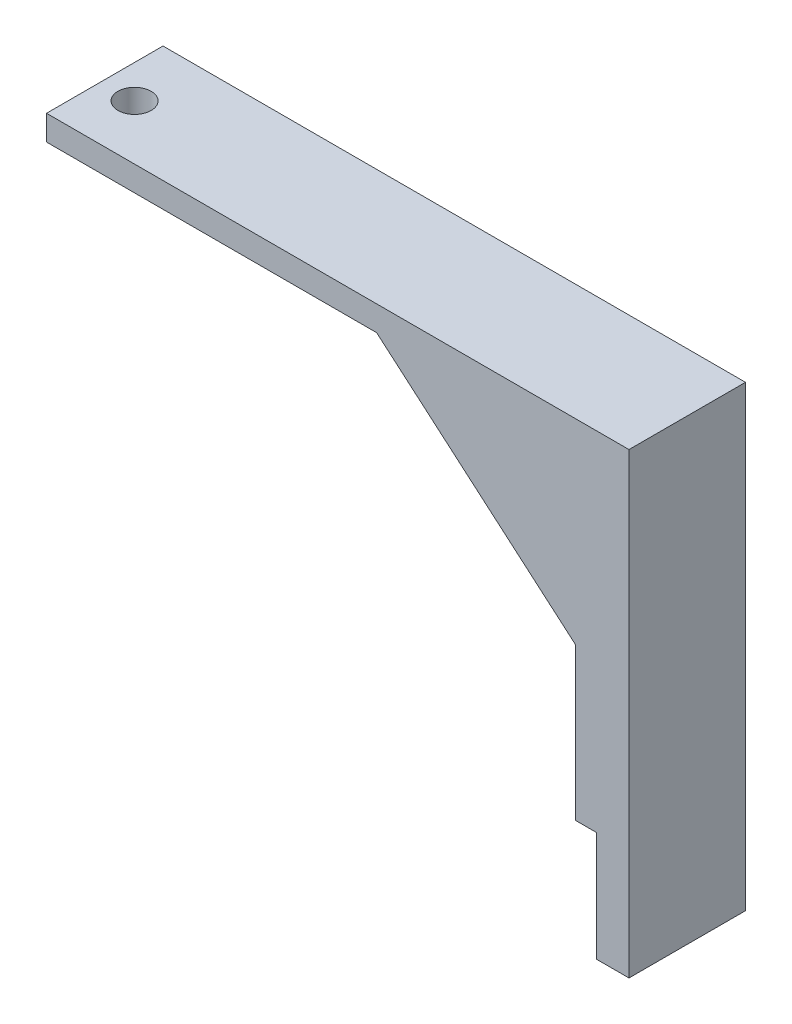
SolidWorks part; units mm, degrees
ref_plane "Front Plane" through (0, 0, 0) normal (0, 0, 1) x (1, 0, 0)
ref_plane "Top Plane" through (0, 0, 0) normal (0, 1, 0) x (1, 0, 0)
ref_plane "Right Plane" through (0, 0, 0) normal (1, 0, 0) x (0, 0, -1)
sketch "Sketch1" plane through (0, 0, 0) normal (0, 0, 1) x (1, 0, 0)
  line L0 (26.0192, -56.9328) -> (33.8256, -56.9328)
  line L1 (33.8256, -56.9328) -> (33.8256, 53.0672)
  line L2 (33.8256, 53.0672) -> (-106.1744, 53.0672)
  line L3 (-106.1744, 53.0672) -> (-106.1744, 47.0672)
  line L4 (-106.1744, 47.0672) -> (-26.8304, 47.0672)
  line L5 (-26.8304, 47.0672) -> (21.0192, 5.9856)
  line L6 (21.0192, 5.9856) -> (21.0192, -30.5571)
  line L8 (21.0192, -30.5571) -> (26.0192, -30.5571)
  line L11 (26.0192, -30.5571) -> (26.0192, -56.9328)
  dimension "D1" = 5
  dimension "D2" = 26.3757
  dimension "D3" = 110
  dimension "D4" = 6
  dimension "D5" = 140
extrude "Extrude1" add sketch "Sketch1" along normal blind 28
sketch "Sketch2" plane through (0, 53.0672, 0) normal (0, 1, 0) x (-1, 0, 0)
  line L0 (106.1744, 28) -> (106.1744, 0) construction
  circle A0 centre (98.1744, 14.8418) radius 4
  dimension "D1" = 8
  dimension "D2" = 8
extrude "Extrude2" cut sketch "Sketch2" against normal blind 28
